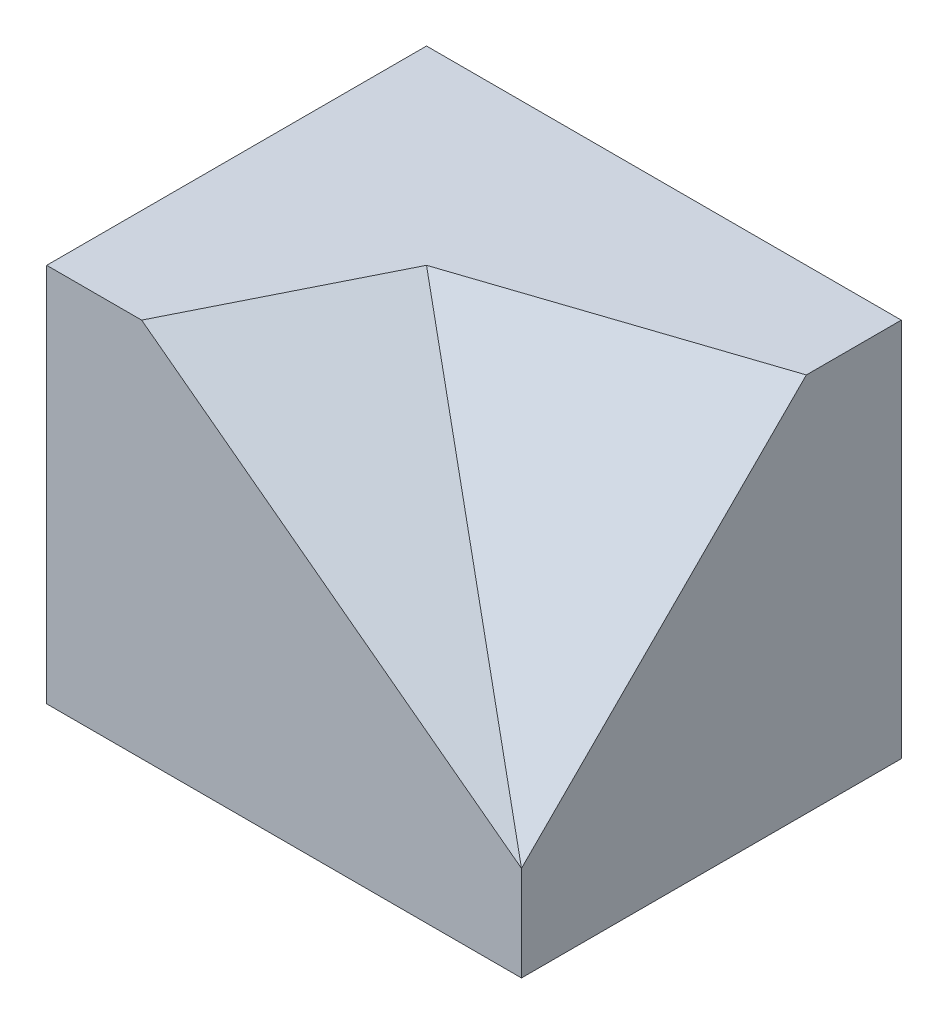
SolidWorks part; units mm, degrees
ref_plane "前基準面" through (0, 0, 0) normal (0, 0, 1) x (1, 0, 0)
ref_plane "上基準面" through (0, 0, 0) normal (0, 1, 0) x (1, 0, 0)
ref_plane "右基準面" through (0, 0, 0) normal (1, 0, 0) x (0, 0, -1)
sketch "草圖1" plane through (0, 0, 0) normal (0, 1, 0) x (1, 0, 0)
  line L1 (12.5, 10) -> (-12.5, 10)
  line L2 (12.5, 10) -> (12.5, -10)
  line L3 (12.5, -10) -> (-12.5, -10)
  line L4 (-12.5, 10) -> (-12.5, -10)
  line L5 (12.5, 10) -> (-12.5, -10) construction
  line L6 (12.5, -10) -> (-12.5, 10) construction
  point P0 (0, 0)
  dimension "D1" = 20
  dimension "D2" = 25
extrude "填料-伸長1" add sketch "草圖1" along normal blind 20
sketch "草圖2" plane through (0, 20, 0) normal (0, 1, 0) x (1, 0, 0)
  line L0 (12.5, -10) -> (-2.5, 0)
  line L1 (-2.5, 0) -> (-7.5, -10)
  line L2 (-12.5, -10) -> (12.5, -10) construction
  line L3 (-2.5, 0) -> (12.5, 5)
  line L4 (12.5, -10) -> (12.5, 10) construction
  dimension "D1" = 5
  dimension "D2" = 15
  dimension "D3" = 10
  dimension "D4" = 5
sketch "草圖3" plane through (0, 0, 10) normal (0, 0, 1) x (1, 0, 0)
  line L0 (-7.5, 20) -> (12.5, 5)
  line L1 (-12.5, 20) -> (12.5, 20) construction
  line L2 (-2.5, 20) -> (-7.5, 20) construction
  line L3 (12.5, 20) -> (12.5, 0) construction
  line L4 (12.5, 5) -> (-2.5, 20)
  dimension "D1" = 5
  dimension "D2" = 15
  dimension "D3" = 5
sketch "草圖4" plane through (12.5, 0, 0) normal (1, 0, 0) x (0, 0, -1)
  line L0 (0, 20) -> (-10, 5)
  line L1 (0, 20) -> (-10, 20) construction
  line L2 (0, 20) -> (5, 20) construction
  line L3 (-10, 20) -> (-10, 0) construction
  line L4 (-10, 5) -> (5, 20)
  line L5 (-10, 20) -> (10, 20) construction
  dimension "D1" = 5
ref_plane "平面2" through (7.9817, 10.6422, 3.9908) normal (-0.5747, -0.7663, -0.2873) x (-0.8184, 0.5381, 0.2018)
sketch "草圖5" plane through (7.9817, 10.6422, 3.9908) normal (-0.5747, -0.7663, -0.2873) x (-0.8184, 0.5381, 0.2018)
  line L2 (18.9177, -2.3408) -> (-5.5212, -7.6077) construction
  line L3 (12.808, 7.0225) -> (18.9177, -2.3408) construction
  line L6 (18.9177, -2.3408) -> (-5.5212, -7.6077)
  line L7 (12.808, 7.0225) -> (18.9177, -2.3408)
  line L8 (12.808, 7.0225) -> (-5.5212, -7.6077)
extrude "除料-伸長1" cut sketch "草圖5" against normal blind 20
ref_plane "平面3" through (3.0263, 9.0789, 9.0789) normal (0.2294, 0.6882, 0.6882) x (0.9733, -0.1622, -0.1622)
sketch "草圖7" plane through (3.0263, 9.0789, 9.0789) normal (0.2294, 0.6882, 0.6882) x (0.9733, -0.1622, -0.1622)
  line L0 (9.7333, -3.5355) -> (9.7333, 17.6777) construction
  line L1 (-5.6777, 14.1421) -> (9.7333, 17.6777) construction
  line L2 (9.7333, -3.5355) -> (9.7333, 17.6777)
  line L3 (-5.6777, 14.1421) -> (9.7333, 17.6777)
  line L4 (-5.6777, 14.1421) -> (9.7333, -3.5355)
extrude "除料-伸長5" cut sketch "草圖7" along normal blind 20
scale "縮放比例1" scale about centroid uniform scaling yes scale factor 0.2
